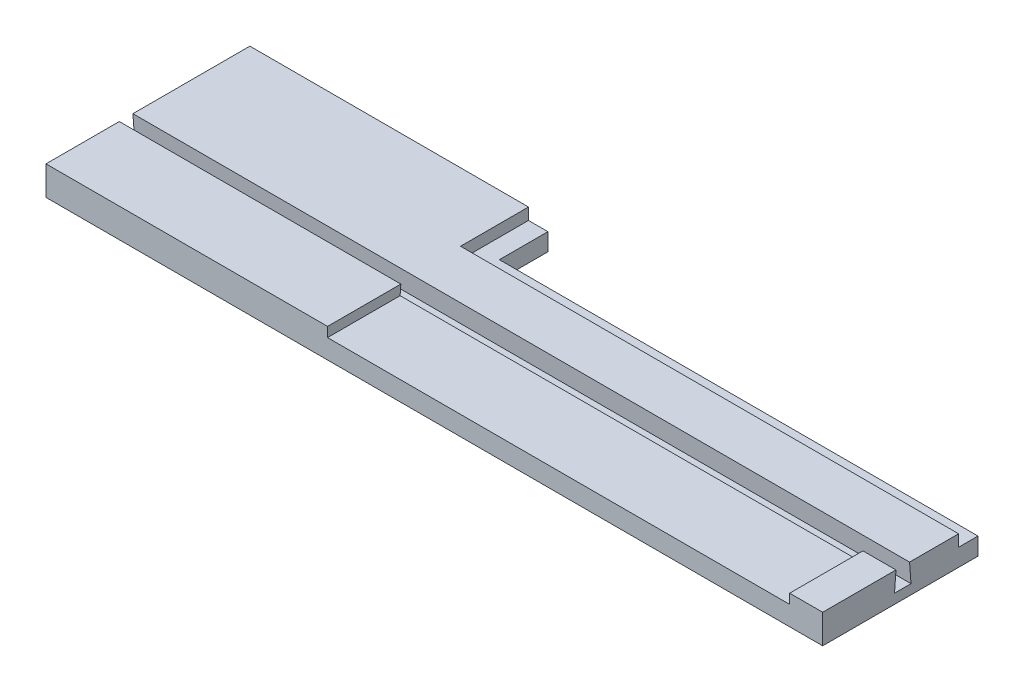
SolidWorks part; units mm, degrees
ref_plane "Front Plane" through (0, 0, 0) normal (0, 0, 1) x (1, 0, 0)
ref_plane "Top Plane" through (0, 0, 0) normal (0, 1, 0) x (1, 0, 0)
ref_plane "Right Plane" through (0, 0, 0) normal (1, 0, 0) x (0, 0, -1)
sketch "Sketch1" plane through (0, 0, 0) normal (0, 1, 0) x (1, 0, 0)
  line L1 (-7.5455, 9.1364) -> (72.4545, 9.1364)
  line L2 (-7.5455, 9.1364) -> (-7.5455, -4.8636)
  line L3 (-7.5455, -4.8636) -> (72.4545, -4.8636)
  line L4 (72.4545, 9.1364) -> (72.4545, -4.8636)
  dimension "D1" = 14
  dimension "D2" = 80
extrude "Boss-Extrude1" add sketch "Sketch1" along normal blind 2
sketch "Sketch2" plane through (0, 2, 0) normal (0, 1, 0) x (1, 0, 0)
  line L0 (72.4545, -4.8636) -> (72.4545, 9.1364) construction
  line L1 (-7.5455, -4.8636) -> (72.4545, -4.8636)
  line L2 (-7.5455, -4.8636) -> (-7.5455, 2.5364)
  line L3 (-7.5455, 2.5364) -> (72.4545, 2.5364)
  line L4 (72.4545, -4.8636) -> (72.4545, 2.5364)
  line L7 (-7.5455, 9.1364) -> (72.4545, 9.1364)
  line L8 (-7.5455, 9.1364) -> (-7.5455, 4.2364)
  line L9 (-7.5455, 4.2364) -> (72.4545, 4.2364)
  line L10 (72.4545, 9.1364) -> (72.4545, 4.2364)
  dimension "D1" = 7.4
  dimension "D2" = 1.7
  dimension "D3" = 4.9
extrude "Boss-Extrude2" add sketch "Sketch2" along normal blind 2 contours L3 L4 L1 L2 | L8 L9 L10 L7
sketch "Sketch3" plane through (0, 0, 0) normal (0, -1, 0) x (1, 0, 0)
  line L0 (72.4545, 4.8636) -> (72.4545, -9.1364) construction
  line L1 (-7.5455, -9.1364) -> (21.1545, -9.1364)
  line L2 (-7.5455, -9.1364) -> (-7.5455, -16.1364)
  line L3 (-7.5455, -16.1364) -> (21.1545, -16.1364)
  line L4 (21.1545, -9.1364) -> (21.1545, -16.1364)
  dimension "D1" = 7
  dimension "D2" = 51.3
extrude "Boss-Extrude3" add sketch "Sketch3" against normal up to surface (4 mm away) up to face at (32.4545, 4, -6.6864)
sketch "Sketch4" plane through (-7.5455, 0, 0) normal (-1, 0, 0) x (0, 0, 1)
  line L0 (-4.2364, 4) -> (-2.5364, 4) construction
  line L1 (-2.5364, 2) -> (-2.6864, 4)
  line L2 (-2.6864, 4) -> (-2.5364, 4)
  line L3 (-2.5364, 4) -> (-2.5364, 2)
  line L4 (-4.2364, 2) -> (-4.2364, 4)
  line L5 (-4.2364, 4) -> (-4.0864, 4)
  line L6 (-4.0864, 4) -> (-4.2364, 2)
  dimension "D1" = 0.15
  dimension "D2" = 0.15
extrude "Boss-Extrude4" add sketch "Sketch4" against normal up to surface (80 mm away) up to face at (72.4545, 2.5, -2.7614)
sketch "Sketch5" plane through (0, 0, 0) normal (0, -1, 0) x (1, 0, 0)
  line L0 (-7.5455, 4.8636) -> (72.4545, 4.8636)
  line L1 (72.4545, 4.8636) -> (72.4545, -9.1364)
  line L2 (72.4545, -9.1364) -> (21.1545, -9.1364)
  line L3 (21.1545, -9.1364) -> (21.1545, -16.1364)
  line L4 (21.1545, -16.1364) -> (-7.5455, -16.1364)
  line L5 (-7.5455, -16.1364) -> (-7.5455, 4.8636)
extrude "Cut-Extrude1" cut sketch "Sketch5" against normal blind 1
sketch "Sketch6" plane through (0, 1, 0) normal (0, -1, 0) x (1, 0, 0)
  line L1 (21.1545, -9.1364) -> (72.4545, -9.1364)
  line L2 (21.1545, -9.1364) -> (21.1545, -11.1364)
  line L3 (23.1545, -11.1364) -> (72.4545, -11.1364)
  line L4 (72.4545, -9.1364) -> (72.4545, -11.1364)
  line L5 (21.1545, -16.1364) -> (23.1545, -16.1364)
  line L6 (21.1545, -16.1364) -> (21.1545, -11.1364)
  line L8 (23.1545, -16.1364) -> (23.1545, -11.1364)
  line L9 (72.4545, -9.1364) -> (72.4545, 4.8636) construction
  dimension "D1" = 2
  dimension "D2" = 2
  dimension "D3" = 0
extrude "Boss-Extrude5" add sketch "Sketch6" against normal blind 1.8
sketch "Sketch7" plane through (0, 4, 0) normal (0, 1, 0) x (1, 0, 0)
  line L0 (-7.5455, -4.8636) -> (72.4545, -4.8636) construction
  line L1 (69.0545, -4.8636) -> (21.4545, -4.8636)
  line L2 (69.0545, -4.8636) -> (69.0545, 2.6864)
  line L3 (69.0545, 2.6864) -> (21.4545, 2.6864)
  line L4 (21.4545, -4.8636) -> (21.4545, 2.6864)
  line L5 (72.4545, 2.6864) -> (-7.5455, 2.6864) construction
  line L6 (72.4545, -4.8636) -> (72.4545, 2.6864) construction
  line L7 (-7.5455, -4.8636) -> (-7.5455, 2.6864) construction
  dimension "D1" = 3.4
  dimension "D2" = 29
extrude "Cut-Extrude2" cut sketch "Sketch7" against normal blind 1
